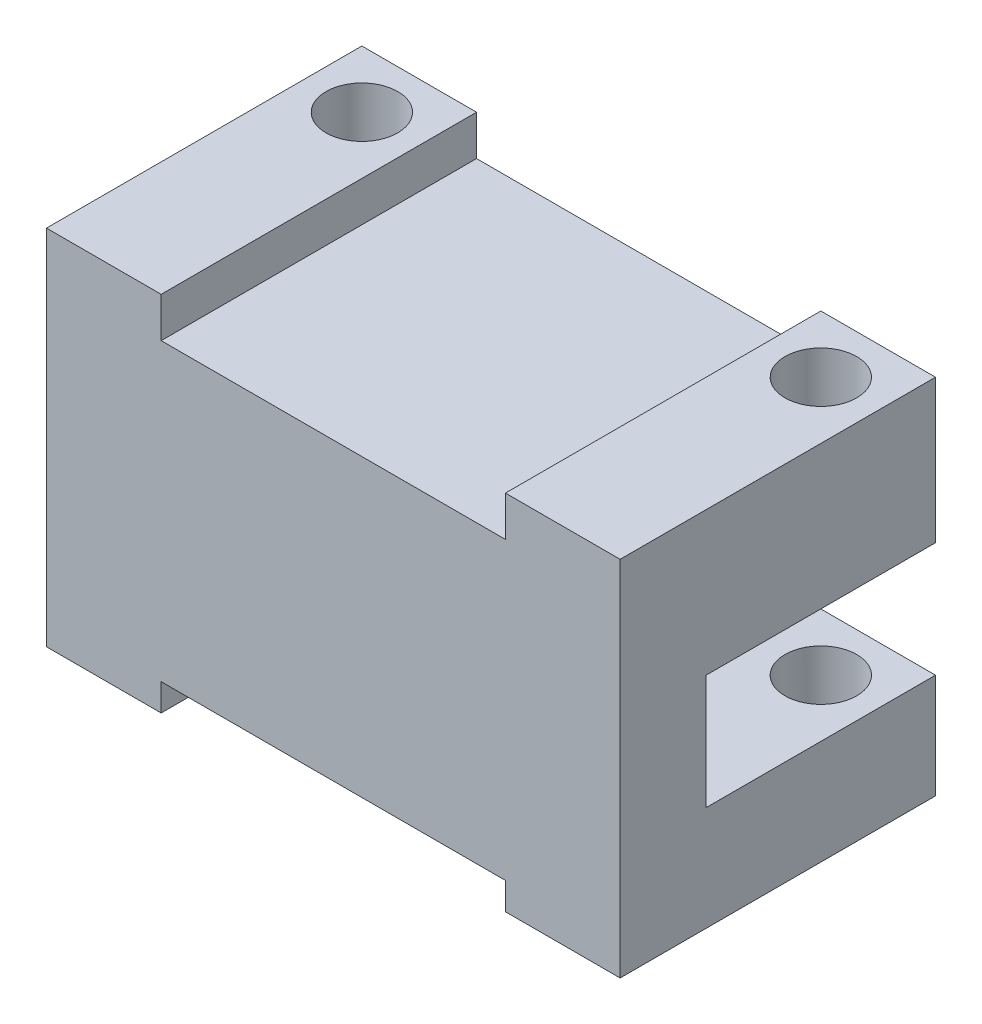
SolidWorks part; units mm, degrees
ref_plane "Front Plane" through (0, 0, 0) normal (0, 0, 1) x (1, 0, 0)
ref_plane "Top Plane" through (0, 0, 0) normal (0, 1, 0) x (1, 0, 0)
ref_plane "Right Plane" through (0, 0, 0) normal (1, 0, 0) x (0, 0, -1)
sketch "Sketch1" plane through (0, 0, 0) normal (0, 0, 1) x (1, 0, 0)
  line L0 (24.6185, -84.9027) -> (24.6185, -85.8498)
  line L1 (36.6261, -85.8498) -> (36.6261, -84.9027)
  line L2 (40.6261, -85.8498) -> (40.6261, -73.2027)
  line L3 (20.6185, -73.2027) -> (20.6185, -85.8498)
  line L6 (36.6261, -84.9027) -> (24.6185, -84.9027)
  line L8 (36.6261, -91.3148) -> (36.6261, -85.5592) construction
  line L10 (20.6185, -85.8498) -> (24.6185, -85.8498)
  line L11 (40.6261, -91.3148) -> (40.6261, -85.5592) construction
  line L14 (20.6185, -85.7535) -> (20.6185, -95.8462) construction
  line L15 (20.6185, -73.2027) -> (40.6261, -73.2027)
  line L16 (24.6185, -85.7535) -> (24.6185, -95.8462) construction
  line L18 (36.6261, -85.8498) -> (40.6261, -85.8498)
  dimension "D2" = 4
extrude "Boss-Extrude1" add sketch "Sketch1" along normal blind 3
sketch "Sketch2" plane through (0, 0, 0) normal (0, 0, -1) x (-1, 0, 0)
  line L0 (-40.6261, -73.2027) -> (-20.6185, -73.2027) construction
  line L1 (-40.6261, -73.2027) -> (-20.6185, -73.2027)
  line L2 (-40.6261, -73.2027) -> (-40.6261, -78.2027)
  line L3 (-40.6261, -78.2027) -> (-20.6185, -78.2027)
  line L4 (-20.6185, -73.2027) -> (-20.6185, -78.2027)
  line L5 (-20.6185, -73.2027) -> (-20.6185, -85.8498) construction
extrude "Boss-Extrude2" add sketch "Sketch2" along normal blind 8
sketch "Sketch3" plane through (0, 0, 0) normal (0, 0, -1) x (-1, 0, 0)
  line L8 (-20.6185, -78.2027) -> (-40.6261, -78.2027)
  line L9 (-40.6261, -78.2027) -> (-40.6261, -85.8498)
  line L10 (-40.6261, -85.8498) -> (-36.6261, -85.8498)
  line L11 (-36.6261, -85.8498) -> (-36.6261, -84.9027)
  line L12 (-36.6261, -84.9027) -> (-24.6185, -84.9027)
  line L13 (-24.6185, -84.9027) -> (-24.6185, -85.8498)
  line L14 (-24.6185, -85.8498) -> (-20.6185, -85.8498)
  line L15 (-20.6185, -85.8498) -> (-20.6185, -78.2027)
  line L17 (-40.6261, -82.2027) -> (-40.6261, -85.8498)
  line L18 (-40.6261, -85.8498) -> (-36.6261, -85.8498)
  line L19 (-36.6261, -85.8498) -> (-36.6261, -84.9027)
  line L20 (-36.6261, -84.9027) -> (-24.6185, -84.9027)
  line L21 (-24.6185, -84.9027) -> (-24.6185, -85.8498)
  line L22 (-24.6185, -85.8498) -> (-20.6185, -85.8498)
  line L23 (-20.6185, -85.8498) -> (-20.6185, -82.2027)
  line L24 (-40.6261, -82.2027) -> (-20.6185, -82.2027)
  dimension "D1" = 0
extrude "Boss-Extrude3" add sketch "Sketch3" along normal blind 8
sketch "Sketch4" plane through (0, 0, 3) normal (0, 0, 1) x (1, 0, 0)
  line L0 (40.6261, -73.2027) -> (20.6185, -73.2027) construction
  line L1 (24.6185, -73.2027) -> (36.6261, -73.2027)
  line L2 (24.6185, -73.2027) -> (24.6185, -74.6027)
  line L3 (24.6185, -74.6027) -> (36.6261, -74.6027)
  line L4 (36.6261, -73.2027) -> (36.6261, -74.6027)
  dimension "D1" = 1.4
extrude "Cut-Extrude1" cut sketch "Sketch4" against normal blind 27.7
hole_wizard "Tap Drill for M3 Tap1" positions "Sketch6" profile "Sketch5" hole size "M3" standard "ISO"
sketch "Sketch6" plane through (0, -73.2027, 0) normal (0, 1, 0) x (1, 0, 0)
  line L0 (20.6185, -3) -> (20.6185, 8) construction
  line L1 (40.6261, -3) -> (40.6261, 8) construction
  line L2 (36.6261, 8) -> (40.6261, 8) construction
  line L3 (20.6185, 8) -> (24.6185, 8) construction
  point P0 (22.6185, 6)
  point P2 (38.6261, 6)
  dimension "D1" = 2
  dimension "D2" = 2
  dimension "D3" = 2
  dimension "D4" = 2
sketch "Sketch5" plane through (22.6185, -73.2027, -6) normal (1, 0, 0) x (0, 0, 1)
  line L0 (0, 0) -> (0, 16.2511)
  line L1 (0, 16.2511) -> (1.25, 15.5)
  line L2 (1.25, 15.5) -> (1.25, 0)
  line L5 (1.25, 0) -> (0, 0)
  line L10 (0, 16.2511) -> (-1.25, 15.5) construction
  line L11 (0, -6.35) -> (0, 107.95) construction
  dimension "Hole Dia." = 2.5
  dimension "Hole Depth" = 15.5
  dimension "Drill Angle" = 118
